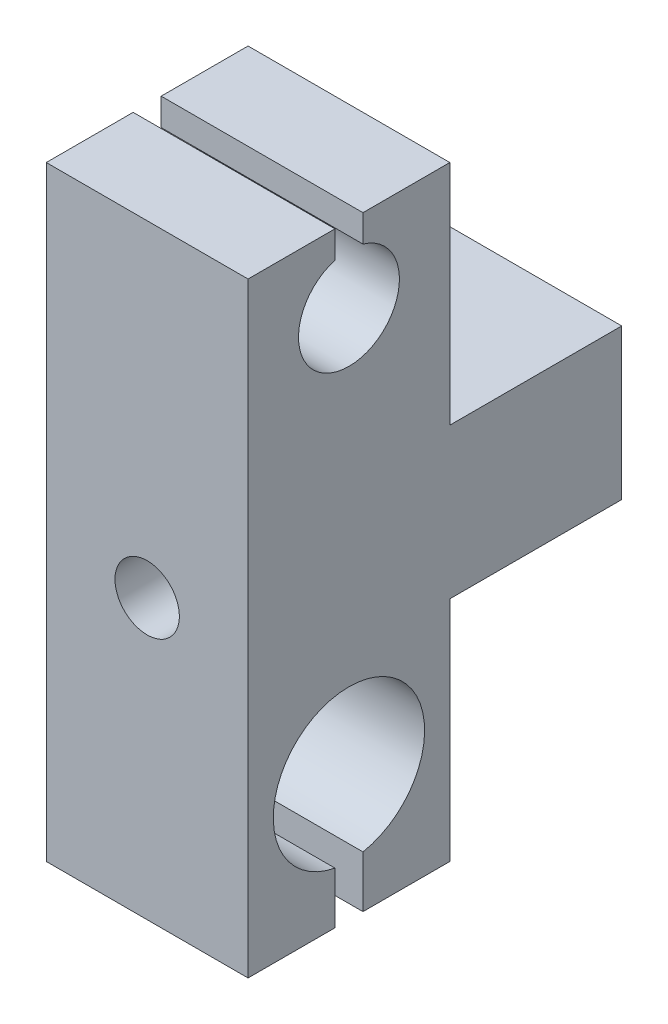
SolidWorks part; units mm, degrees
material "6061-T6 (SS)"
ref_plane "Front Plane" through (0, 0, 0) normal (0, 0, 1) x (1, 0, 0)
ref_plane "Top Plane" through (0, 0, 0) normal (0, 1, 0) x (1, 0, 0)
ref_plane "Right Plane" through (0, 0, 0) normal (1, 0, 0) x (0, 0, -1)
sketch "Sketch1" plane through (0, 0, 0) normal (1, 0, 0) x (0, 0, -1)
  line L0 (0, 0) -> (0, 28.575) construction
  line L1 (0, 0) -> (0, -22.225) construction
  line L2 (-1.7648, 38.1) -> (-1.7648, 34.6748)
  line L3 (12.7, -38.1) -> (1.7648, -38.1)
  line L4 (12.7, -38.1) -> (12.7, -9.4665)
  line L5 (12.7, 38.1) -> (1.7648, 38.1)
  line L6 (-12.7, -38.1) -> (-12.7, 38.1)
  line L7 (12.7, -38.1) -> (-12.7, 38.1) construction
  line L8 (12.7, 38.1) -> (-12.7, -38.1) construction
  line L9 (1.7648, 38.1) -> (1.7648, 34.6748)
  line L10 (-1.7648, 34.6748) -> (-1.7648, -31.5851) construction
  line L11 (-1.7648, -31.5851) -> (-1.7648, -38.1)
  line L12 (1.7648, -31.5851) -> (1.7648, -38.1)
  line L13 (-1.7648, 38.1) -> (-12.7, 38.1)
  line L14 (-1.7648, -38.1) -> (-12.7, -38.1)
  line L15 (0, 0) -> (41.0367, 0) construction
  line L16 (12.7, 9.4665) -> (12.7, 38.1)
  line L17 (34.3377, -9.4665) -> (12.7, -9.4665)
  line L18 (34.3377, -9.4665) -> (34.3377, 9.4665)
  line L19 (34.3377, 9.4665) -> (12.7, 9.4665)
  line L21 (34.3377, -9.4665) -> (12.7, 9.4665) construction
  line L22 (34.3377, 9.4665) -> (12.7, -9.4665) construction
  line L23 (34.3377, 1.0472) -> (34.3377, -7.0528) construction
  arc A0 (-1.7648, 34.6748) -> (1.7648, 34.6748) centre (0, 28.575) ccw
  arc A1 (1.7648, -31.5851) -> (-1.7648, -31.5851) centre (0, -22.225) ccw
  point P3 (23.5189, 0)
  dimension "D3" = 12.7
  dimension "D4" = 19.05
  dimension "D1" = 22.225
  dimension "D2" = 28.575
  dimension "D5" = 76.2
  dimension "D6" = 25.4
extrude "Boss-Extrude1" add sketch "Sketch1" along normal blind 25.4
sketch "Sketch3" plane through (0, 0, -34.3377) normal (0, 0, -1) x (-1, 0, 0)
  line L0 (-25.4, -3.0028) -> (0, -3.0028) construction
  line L1 (0, -9.4665) -> (0, 9.4665) construction
  line L2 (-25.4, -9.4665) -> (-25.4, 9.4665) construction
  circle A0 centre (-12.7, -3.0028) radius 4.05
  point P6 (-12.7, -3.0028)
extrude "Cut-Extrude1" cut sketch "Sketch3" against normal through all
